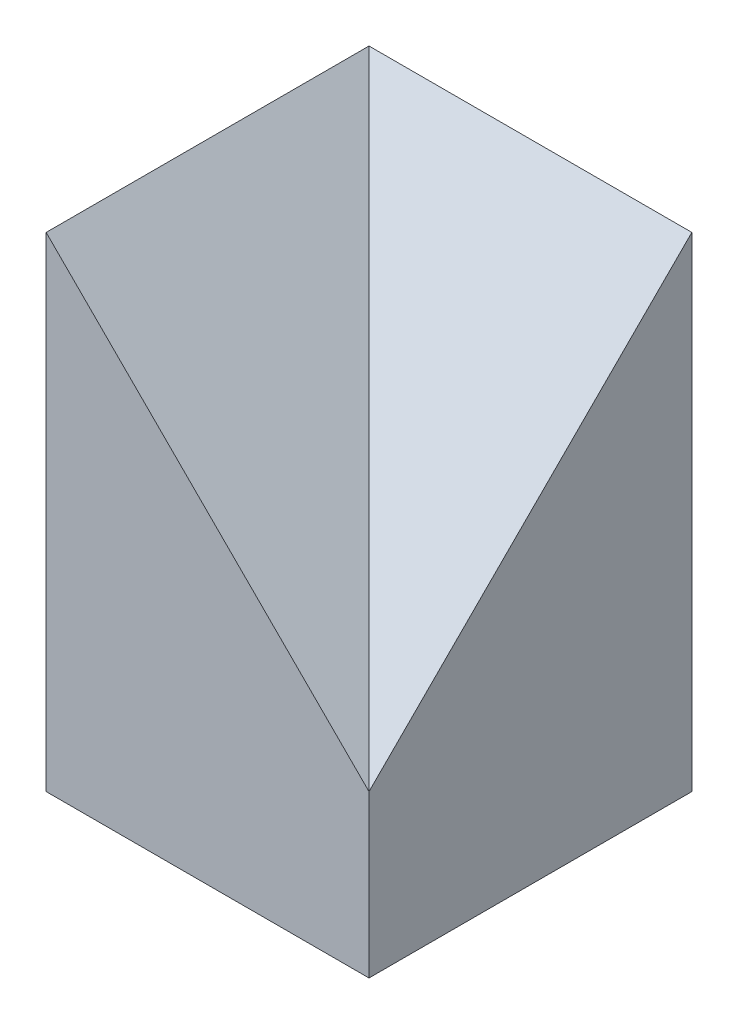
SolidWorks part; units mm, degrees
ref_plane "Ebene vorne" through (0, 0, 0) normal (0, 0, 1) x (1, 0, 0)
ref_plane "Ebene oben" through (0, 0, 0) normal (0, 1, 0) x (1, 0, 0)
ref_plane "Ebene rechts" through (0, 0, 0) normal (1, 0, 0) x (0, 0, -1)
sketch "Skizze1" plane through (0, 0, 0) normal (0, 1, 0) x (1, 0, 0)
  line L1 (0, 0) -> (400, 0)
  line L2 (0, 0) -> (0, -400)
  line L3 (0, -400) -> (400, -400)
  line L4 (400, 0) -> (400, -400)
  dimension "D1" = 400
extrude "Aufsatz-Linear austragen1" add sketch "Skizze1" along normal blind 200
sketch "Skizze2" plane through (0, 200, 0) normal (0, 1, 0) x (1, 0, 0)
  line L1 (0, 0) -> (400, 0)
  line L2 (0, 0) -> (0, -400)
  line L3 (0, -400) -> (400, -400)
  line L4 (400, 0) -> (400, -400)
ref_plane "Ebene1" through (0, 600, 0) normal (0, 1, 0) x (1, 0, 0)
sketch "Skizze3" plane through (0, 600, 0) normal (0, 1, 0) x (1, 0, 0)
  line L0 (0, -400) -> (400, -400) construction
  line L1 (400, 0) -> (400, -400) construction
  line L2 (0, 0) -> (400, 0) construction
  line L3 (0, 0) -> (0, -400) construction
  line L4 (0, -400) -> (400, -400)
  line L5 (400, 0) -> (400, -400)
  line L6 (0, 0) -> (400, 0)
  line L7 (0, 0) -> (0, -400)
  point P4 (0, 0)
sketch3d "3D-Skizze2"
  line L1 (400, 200, 400) -> (0, 200, 400)
  line L2 (0, 200, 0) -> (0, 200, 400)
  line L3 (400, 200, 0) -> (0, 200, 0)
  line L4 (0, 600, 0) -> (0, 200, 0)
  line L7 (400, 200, 400) -> (400, 200, 0)
  line L8 (400, 600, 0) -> (400, 200, 0)
  line L9 (400, 200, 400) -> (400, 600, 0)
  line L10 (400, 200, 400) -> (0, 600, 400)
  line L11 (0, 600, 400) -> (0, 200, 400)
  line L12 (0, 600, 400) -> (0, 600, 0)
  line L13 (400, 600, 0) -> (0, 600, 0)
  line L14 (400, 200, 400) -> (0, 600, 0)
sketch "Skizze4" plane through (0, 200, 0) normal (0, 1, 0) x (1, 0, 0)
  point P0 (400, -400)
extrude "Aufsatz-Linear austragen2" add sketch "Skizze2" along normal up to vertex (400 mm away) up to point (0, 600, 0)
loft "Schnitt-Ausformung1" cut profiles "Skizze3", "Skizze4"
